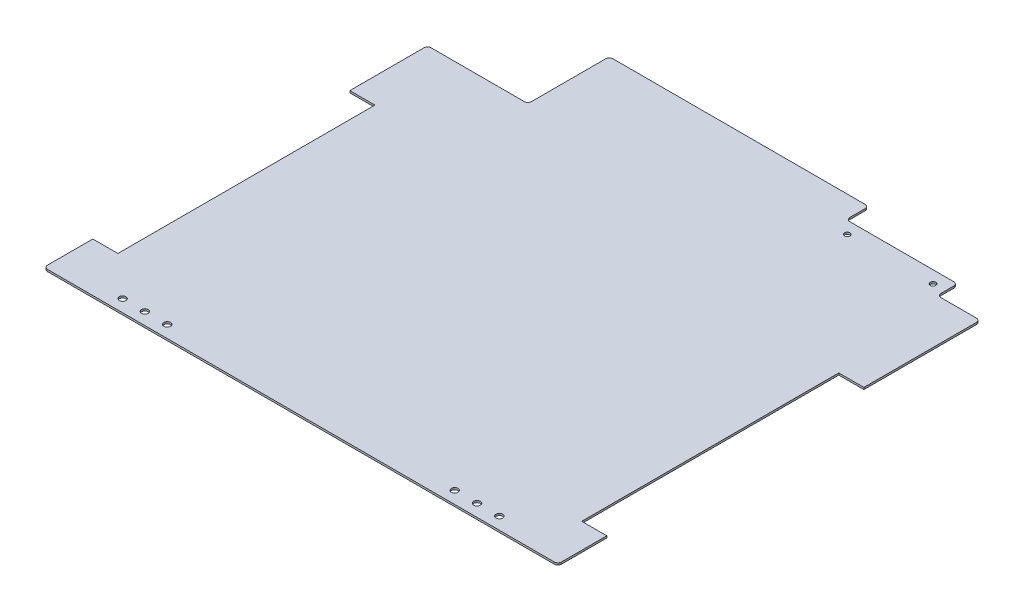
SolidWorks part; units mm, degrees
material "1060 Alloy"
ref_plane "Front Plane" through (0, 0, 0) normal (0, 0, 1) x (1, 0, 0)
ref_plane "Top Plane" through (0, 0, 0) normal (0, 1, 0) x (1, 0, 0)
ref_plane "Right Plane" through (0, 0, 0) normal (1, 0, 0) x (0, 0, -1)
sketch "Sketch1" plane through (0, 0, 0) normal (0, 1, 0) x (1, 0, 0)
  line L1 (91.75, -187.6479) -> (-208.25, -187.6479)
  line L2 (211.75, -157.6275) -> (211.75, 157.3827)
  line L3 (176.75, 192.3725) -> (-117.25, 192.3725)
  line L4 (-208.25, -187.6479) -> (-208.25, 92.9734)
  line L5 (211.75, -187.6479) -> (-207.4548, 183.8417) construction
  line L6 (212.4761, 191.456) -> (-208.25, -187.6479) construction
  line L8 (176.75, 192.3725) -> (176.75, 157.3827)
  line L9 (176.75, 157.3827) -> (211.75, 157.3827)
  line L14 (91.75, -187.6479) -> (211.75, -187.6479)
  line L15 (211.75, -187.6479) -> (211.75, -157.6275)
  line L16 (-198.25, 192.3725) -> (201.75, 192.3725) construction
  line L17 (209.7434, 172.3827) -> (205.0444, 172.3827) construction
  line L18 (-126.25, 125.8725) -> (-126.25, 192.3725)
  line L19 (-126.25, 192.3725) -> (-117.25, 192.3725)
  line L20 (-126.25, 125.8725) -> (-208.25, 125.8725)
  line L21 (-208.25, 125.8725) -> (-208.25, 92.9734)
  point P0 (0, 0)
  dimension "D1" = 420
  dimension "D2" = 15
  dimension "D3" = 82
  dimension "D4" = 35
  dimension "D5" = 91
  dimension "D6" = 66.5
  dimension "D7" = 380.0204
  dimension "D8" = 315.0102
  dimension "D9" = 280.6214
  dimension "D10" = 420
  dimension "D11" = 33.5
  dimension "D12" = 120
extrude "Boss-Extrude1" add sketch "Sketch1" along normal blind 1.5875
sketch "Sketch6" plane through (0, 1.5875, 0) normal (0, 1, 0) x (1, 0, 0)
  line L0 (-208.25, -187.6479) -> (211.75, -187.6479) construction
  line L1 (0, -0.8731) -> (0, 0.8731) construction
  point P0 (-153.9375, -177.6479)
  point P1 (-135.6775, -177.6479)
  point P2 (-117.4175, -177.6479)
  point P8 (153.9375, -177.6479)
  point P9 (135.6775, -177.6479)
  point P10 (117.4175, -177.6479)
  dimension "D1" = 18.26
  dimension "D2" = 18.26
  dimension "D3" = 10
hole_wizard "M5 Clearance Hole1" positions "Sketch9" profile "Sketch10" hole size "M5" standard "ANSI Metric" end condition through all
sketch "Sketch9" plane through (0, 1.5875, 0) normal (0, 1, 0) x (1, 0, 0)
  point P0 (-153.9375, -177.6479)
  point P3 (-135.6775, -177.6479)
  point P6 (-117.4175, -177.6479)
  point P9 (117.4175, -177.6479)
  point P12 (135.6775, -177.6479)
  point P15 (153.9375, -177.6479)
sketch "Sketch10" plane through (-153.9375, 1.5875, 177.6479) normal (1, 0, 0) x (0, 0, 1)
  line L0 (0, 0) -> (0, 1.5875)
  line L1 (0, 1.5875) -> (2.75, 1.5875)
  line L2 (2.75, 1.5875) -> (2.75, 0)
  line L5 (2.75, 0) -> (0, 0)
  line L11 (0, -6.35) -> (0, 107.95) construction
  dimension "Thru Hole Dia." = 5.5
  dimension "Thru Hole Depth" = 1.5875
sketch "Sketch11" plane through (0, 1.5875, 0) normal (0, 1, 0) x (1, 0, 0)
  line L1 (176.75, 192.3725) -> (85.75, 192.3725)
  line L2 (176.75, 192.3725) -> (176.75, 173.8725)
  line L3 (176.75, 173.8725) -> (85.75, 173.8725)
  line L4 (85.75, 192.3725) -> (85.75, 173.8725)
  dimension "D1" = 18.5
  dimension "D2" = 91
extrude "Cut-Extrude1" cut sketch "Sketch11" against normal through all both and the other way through all
sketch "Sketch12" plane through (0, 1.5875, 0) normal (0, 1, 0) x (1, 0, 0)
  line L0 (176.75, 173.8725) -> (85.75, 173.8725) construction
  line L1 (96.75, 163.8725) -> (166.75, 163.8725) construction
  line L2 (176.75, 157.3827) -> (176.75, 173.8725) construction
  point P0 (96.75, 163.8725)
  point P1 (166.75, 163.8725)
  point P6 (131.75, 163.8725)
  dimension "D1" = 70
  dimension "D2" = 10
  dimension "D3" = 45
hole_wizard "M4 Clearance Hole1" positions "Sketch13" profile "Sketch14" hole size "M4" standard "ANSI Metric" end condition through all
sketch "Sketch13" plane through (0, 1.5875, 0) normal (0, 1, 0) x (1, 0, 0)
  point P0 (96.75, 163.8725)
  point P3 (166.75, 163.8725)
sketch "Sketch14" plane through (96.75, 1.5875, -163.8725) normal (1, 0, 0) x (0, 0, 1)
  line L0 (0, 0) -> (0, 1.5875)
  line L1 (0, 1.5875) -> (2.25, 1.5875)
  line L2 (2.25, 1.5875) -> (2.25, 0)
  line L5 (2.25, 0) -> (0, 0)
  line L11 (0, -6.35) -> (0, 107.95) construction
  dimension "Thru Hole Dia." = 4.5
  dimension "Thru Hole Depth" = 1.5875
sketch "Sketch15" plane through (0, 1.5875, 0) normal (0, 1, 0) x (1, 0, 0)
  line L0 (-208.25, 125.8725) -> (-208.25, -187.6479) construction
  line L1 (-208.25, -147.6479) -> (-187.75, -147.6479)
  line L2 (-208.25, -147.6479) -> (-208.25, 62.3521)
  line L3 (-208.25, 62.3521) -> (-187.75, 62.3521)
  line L4 (-187.75, -147.6479) -> (-187.75, 62.3521)
  line L5 (-208.25, -187.6479) -> (211.75, -187.6479) construction
  line L11 (211.75, -187.6479) -> (211.75, 157.3827) construction
  line L12 (211.75, -147.6479) -> (191.25, -147.6479)
  line L13 (211.75, -147.6479) -> (211.75, 62.3521)
  line L14 (211.75, 62.3521) -> (191.25, 62.3521)
  line L15 (191.25, -147.6479) -> (191.25, 62.3521)
  dimension "D1" = 210
  dimension "D2" = 20.5
  dimension "D3" = 40
fillet "Fillet1" radius 3 10 edges at (-208.25, 0.7937, -125.8725) (-126.25, 0.7937, -125.8725) (-126.25, 0.7937, -192.3725) (85.75, 0.7937, -192.3725) (85.75, 0.7937, -173.8725) (176.75, 0.7937, -173.8725) (176.75, 0.7937, -157.3827) (211.75, 0.7937, -157.3827) (211.75, 0.7937, 187.6479) (-208.25, 0.7937, 187.6479)
extrude "Cut-Extrude2" cut sketch "Sketch15" against normal through all both and the other way through all
